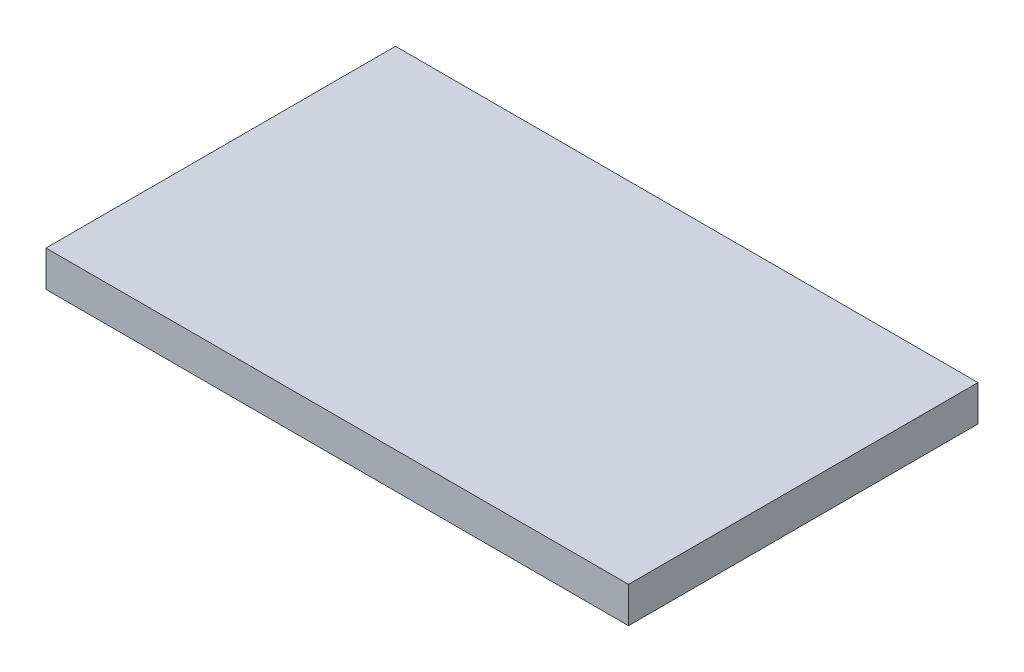
SolidWorks part; units mm, degrees
ref_plane "Plano frontal" through (0, 0, 0) normal (0, 0, 1) x (1, 0, 0)
ref_plane "Plano superior" through (0, 0, 0) normal (0, 1, 0) x (1, 0, 0)
ref_plane "Plano direito" through (0, 0, 0) normal (1, 0, 0) x (0, 0, -1)
sketch "Esboço1" plane through (0, 0, 0) normal (0, 1, 0) x (1, 0, 0)
  line L1 (-16.25, -9.75) -> (16.25, -9.75)
  line L2 (-16.25, -9.75) -> (-16.25, 9.75)
  line L3 (-16.25, 9.75) -> (16.25, 9.75)
  line L4 (16.25, -9.75) -> (16.25, 9.75)
  line L5 (-16.25, -9.75) -> (16.25, 9.75) construction
  line L6 (-16.25, 9.75) -> (16.25, -9.75) construction
  point P0 (0, 0)
  dimension "D1" = 32.5
  dimension "D2" = 19.5
extrude "Ressalto-extrusão1" add sketch "Esboço1" along normal blind 2
